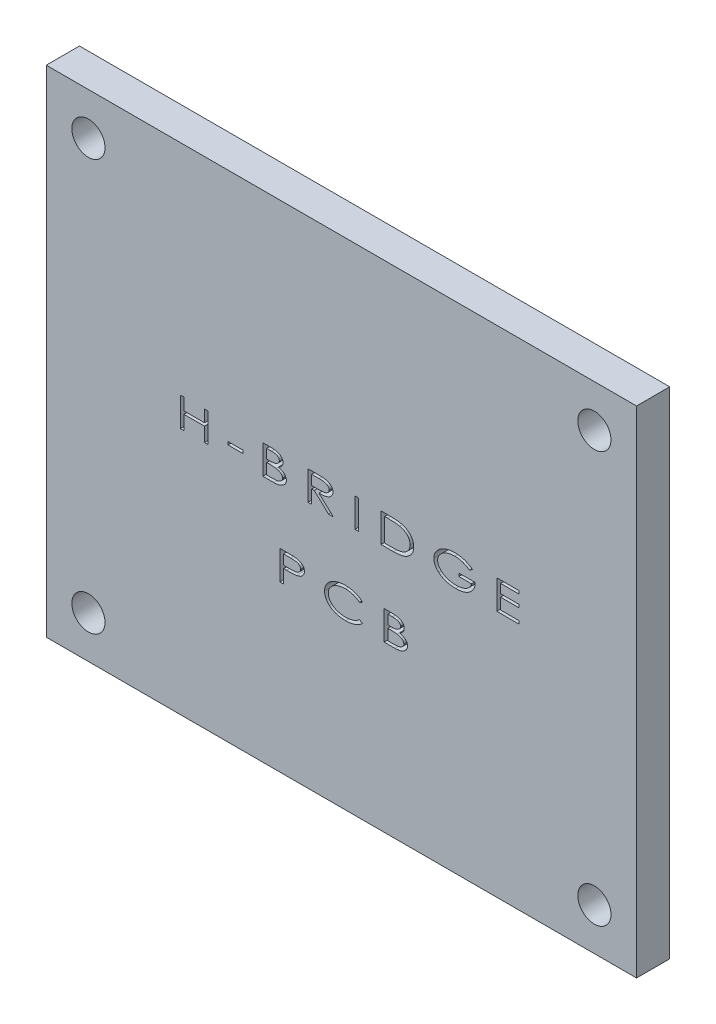
SolidWorks part; units mm, degrees
ref_plane "Front Plane" through (0, 0, 0) normal (0, 0, 1) x (1, 0, 0)
ref_plane "Top Plane" through (0, 0, 0) normal (0, 1, 0) x (1, 0, 0)
ref_plane "Right Plane" through (0, 0, 0) normal (1, 0, 0) x (0, 0, -1)
sketch "Sketch1" plane through (0, 0, 0) normal (0, 0, 1) x (1, 0, 0)
  line L1 (-35.56, 29.845) -> (35.56, 29.845)
  line L2 (-35.56, 29.845) -> (-35.56, -29.845)
  line L3 (-35.56, -29.845) -> (35.56, -29.845)
  line L4 (35.56, 29.845) -> (35.56, -29.845)
  line L5 (-35.56, 29.845) -> (35.56, -29.845) construction
  line L6 (-35.56, -29.845) -> (35.56, 29.845) construction
  circle A0 centre (-30.48, 24.765) radius 2
  circle A1 centre (30.48, 24.765) radius 2
  circle A2 centre (30.48, -24.765) radius 2
  circle A3 centre (-30.48, -24.765) radius 2
  point P0 (0, 0)
  dimension "D3" = 4
  dimension "D8" = 30.48
  dimension "D1" = 71.12
  dimension "D2" = 59.69
  dimension "D4" = 5.08
  dimension "D5" = 5.08
  dimension "D9" = 49.53
  dimension "D6" = 2
  dimension "D7" = 2
extrude "Boss-Extrude1" add sketch "Sketch1" along normal blind 4
sketch "Sketch2" plane through (0, 0, 4) normal (0, 0, 1) x (1, 0, 0)
  line L0 (0, -29.845) -> (0, 29.845) construction
  line L1 (-35.56, -29.845) -> (35.56, -29.845) construction
  line L2 (35.56, 29.845) -> (-35.56, 29.845) construction
  line L3 (-35.56, 0) -> (35.56, 0) construction
  line L4 (-35.56, 29.845) -> (-35.56, -29.845) construction
  line L5 (35.56, -29.845) -> (35.56, 29.845) construction
  text T0 "H-BRIDGE" font "Century Gothic" height 3.5
  text T1 "PCB" font "Century Gothic" height 3.5
  dimension "D1" = 20
  dimension "D2" = 10
  dimension "D3" = 8
extrude "Cut-Extrude1" cut sketch "Sketch2" against normal blind 2
